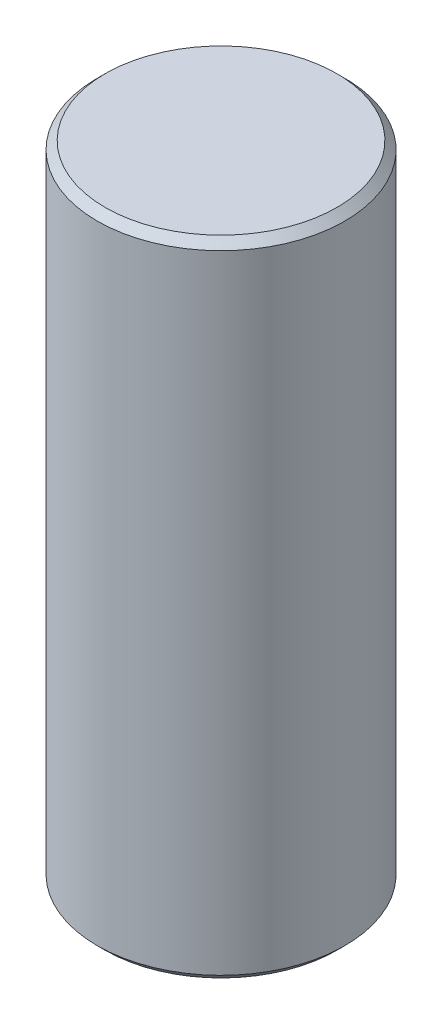
SolidWorks part; units mm, degrees
ref_plane "Front Plane" through (0, 0, 0) normal (0, 0, 1) x (1, 0, 0)
ref_plane "Top Plane" through (0, 0, 0) normal (0, 1, 0) x (1, 0, 0)
ref_plane "Right Plane" through (0, 0, 0) normal (1, 0, 0) x (0, 0, -1)
sketch "Sketch1" plane through (0, 0, 0) normal (0, 1, 0) x (1, 0, 0)
  circle A0 centre (0, 0) radius 7.85
  dimension "D1" = 15.7
extrude "Boss-Extrude1" add sketch "Sketch1" along normal blind 40.8
chamfer "Chamfer1" distance 0.5 angle 45 2 edges at (0, 0, 7.85) (0, 40.8, 7.85)
